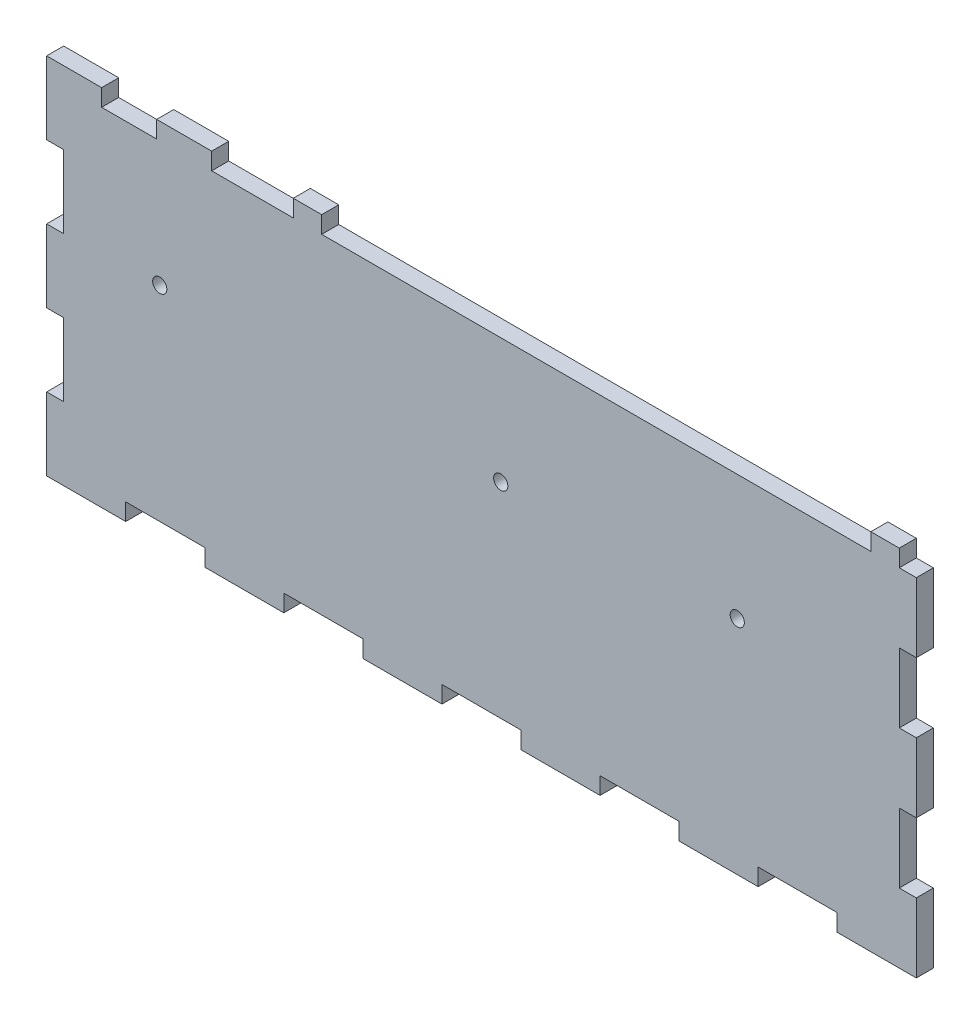
SolidWorks part; units mm, degrees
ref_plane "Alzado" through (0, 0, 0) normal (0, 0, 1) x (1, 0, 0)
ref_plane "Planta" through (0, 0, 0) normal (0, 1, 0) x (1, 0, 0)
ref_plane "Vista lateral" through (0, 0, 0) normal (1, 0, 0) x (0, 0, -1)
sketch "Croquis1" plane through (0, 0, 0) normal (0, 0, 1) x (1, 0, 0)
  line L0 (0, -16.7416) -> (0, -13.7416)
  line L1 (-48.39, -13.7416) -> (0, -13.7416) construction
  line L2 (0, -16.7416) -> (96.61, -16.7416)
  line L3 (101.61, -16.7416) -> (101.61, -49.332) construction
  line L4 (-227.956, -77.7416) -> (93.758, -77.7416) construction
  line L5 (-48.39, -13.7416) -> (-48.39, -77.7416) construction
  line L6 (78.6222, -38.7416) -> (-38.712, -38.7416) construction
  line L7 (0, -13.7416) -> (0, -16.7416) construction
  line L8 (0, -16.7416) -> (-48.39, -16.7416) construction
  line L9 (-48.39, -13.7416) -> (-38.712, -13.7416)
  line L10 (-38.712, -13.7416) -> (-38.712, -16.7416)
  line L11 (-38.712, -16.7416) -> (-29.034, -16.7416)
  line L12 (-29.034, -16.7416) -> (-29.034, -13.7416)
  line L13 (-29.034, -13.7416) -> (-19.356, -13.7416)
  line L14 (-19.356, -13.7416) -> (-19.356, -16.7416)
  line L15 (-19.356, -16.7416) -> (-9.678, -16.7416)
  line L16 (-9.678, -16.7416) -> (-5, -16.7416)
  line L17 (-5, -16.7416) -> (-5, -13.7416)
  line L18 (104.61, -16.7416) -> (104.61, -77.7416) construction
  line L19 (104.61, -16.7416) -> (104.61, -28.9416)
  line L20 (104.61, -28.9416) -> (101.61, -28.9416)
  line L21 (101.61, -28.9416) -> (101.61, -41.1416)
  line L22 (101.61, -41.1416) -> (104.61, -41.1416)
  line L23 (104.61, -41.1416) -> (104.61, -53.3416)
  line L24 (104.61, -53.3416) -> (101.61, -53.3416)
  line L25 (101.61, -53.3416) -> (101.61, -65.5416)
  line L26 (101.61, -65.5416) -> (104.61, -65.5416)
  line L27 (104.61, -65.5416) -> (104.61, -77.7416)
  line L28 (-45.39, -56.5563) -> (-45.39, 45.6638) construction
  line L29 (-48.39, -13.7416) -> (-48.39, -26.5416)
  line L30 (-48.39, -26.5416) -> (-45.39, -26.5416)
  line L31 (-45.39, -26.5416) -> (-45.39, -39.3416)
  line L32 (-45.39, -39.3416) -> (-48.39, -39.3416)
  line L33 (-48.39, -39.3416) -> (-48.39, -52.1416)
  line L34 (-48.39, -52.1416) -> (-45.39, -52.1416)
  line L35 (-45.39, -52.1416) -> (-45.39, -64.9416)
  line L36 (-45.39, -64.9416) -> (-48.39, -64.9416)
  line L37 (-48.39, -64.9416) -> (-48.39, -77.7416)
  line L38 (-102.5031, -74.7416) -> (75.9308, -74.7416) construction
  line L39 (-124.386, -156.1001) -> (179.1879, -156.1001) construction
  line L40 (-48.39, -153.1001) -> (104.61, -153.1001) construction
  line L41 (-48.39, -77.7416) -> (-34.4809, -77.7416)
  line L42 (-34.4809, -77.7416) -> (-34.4809, -74.7416)
  line L43 (-34.4809, -74.7416) -> (-20.5718, -74.7416)
  line L44 (-20.5718, -74.7416) -> (-20.5718, -77.7416)
  line L45 (-20.5718, -77.7416) -> (-6.6627, -77.7416)
  line L46 (-6.6627, -77.7416) -> (-6.6627, -74.7416)
  line L47 (-6.6627, -74.7416) -> (7.2464, -74.7416)
  line L48 (7.2464, -74.7416) -> (7.2464, -77.7416)
  line L49 (7.2464, -77.7416) -> (21.1555, -77.7416)
  line L50 (21.1555, -77.7416) -> (21.1555, -74.7416)
  line L51 (21.1555, -74.7416) -> (35.0645, -74.7416)
  line L52 (35.0645, -74.7416) -> (35.0645, -77.7416)
  line L53 (35.0645, -77.7416) -> (48.9736, -77.7416)
  line L54 (48.9736, -77.7416) -> (48.9736, -74.7416)
  line L55 (48.9736, -74.7416) -> (62.8827, -74.7416)
  line L56 (62.8827, -74.7416) -> (62.8827, -77.7416)
  line L57 (62.8827, -77.7416) -> (76.7918, -77.7416)
  line L58 (76.7918, -77.7416) -> (76.7918, -74.7416)
  line L59 (76.7918, -74.7416) -> (90.7009, -74.7416)
  line L60 (90.7009, -74.7416) -> (90.7009, -77.7416)
  line L61 (90.7009, -77.7416) -> (104.61, -77.7416)
  line L62 (-48.39, -153.1001) -> (-48.39, -260.7101) construction
  line L63 (-48.39, -260.7101) -> (104.61, -260.7101) construction
  line L64 (104.61, -153.1001) -> (104.61, -260.7101) construction
  line L65 (-68.7634, -257.7101) -> (144.8732, -257.7101) construction
  line L66 (101.61, -77.7416) -> (101.61, -269.1968) construction
  line L67 (-45.39, -153.1001) -> (-45.39, -251.8965) construction
  line L68 (-34.4809, -77.7416) -> (-34.4809, -243.0877) construction
  line L69 (-20.5718, -77.7416) -> (-20.5718, -243.0877) construction
  line L70 (-6.6627, -74.7416) -> (-6.6627, -243.0877) construction
  line L71 (7.2464, -74.7416) -> (7.2464, -243.0877) construction
  line L72 (21.1555, -74.7416) -> (21.1555, -243.0877) construction
  line L73 (35.0645, -74.7416) -> (35.0645, -243.0877) construction
  line L74 (48.9736, -74.7416) -> (48.9736, -243.0877) construction
  line L75 (62.8827, -74.7416) -> (62.8827, -243.0877) construction
  line L76 (76.7918, -74.7416) -> (76.7918, -243.0877) construction
  line L77 (90.7009, -74.7416) -> (90.7009, -243.0877) construction
  line L78 (-34.4809, -156.1001) -> (-48.39, -156.1001)
  line L79 (-34.4809, -156.1001) -> (-34.4809, -153.1001)
  line L80 (-34.4809, -153.1001) -> (-20.5718, -153.1001)
  line L81 (-20.5718, -153.1001) -> (-20.5718, -156.1001)
  line L82 (-20.5718, -156.1001) -> (-6.6627, -156.1001)
  line L83 (-6.6627, -156.1001) -> (-6.6627, -153.1001)
  line L84 (-6.6627, -153.1001) -> (7.2464, -153.1001)
  line L85 (7.2464, -153.1001) -> (7.2464, -156.1001)
  line L86 (7.2464, -156.1001) -> (21.1555, -156.1001)
  line L87 (21.1555, -156.1001) -> (21.1555, -153.1001)
  line L88 (21.1555, -153.1001) -> (35.0645, -153.1001)
  line L89 (35.0645, -153.1001) -> (35.0645, -156.1001)
  line L90 (35.0645, -156.1001) -> (48.9736, -156.1001)
  line L91 (48.9736, -156.1001) -> (48.9736, -153.1001)
  line L92 (48.9736, -153.1001) -> (62.8827, -153.1001)
  line L93 (62.8827, -153.1001) -> (62.8827, -156.1001)
  line L94 (62.8827, -156.1001) -> (76.7918, -156.1001)
  line L95 (76.7918, -156.1001) -> (76.7918, -153.1001)
  line L96 (76.7918, -153.1001) -> (90.7009, -153.1001)
  line L97 (90.7009, -153.1001) -> (90.7009, -156.1001)
  line L98 (90.7009, -156.1001) -> (104.61, -156.1001)
  line L99 (-48.39, -257.7101) -> (-34.4809, -257.7101)
  line L100 (-34.4809, -257.7101) -> (-34.4809, -260.7101)
  line L101 (-34.4809, -260.7101) -> (-20.5718, -260.7101)
  line L102 (-20.5718, -260.7101) -> (-20.5718, -257.7101)
  line L103 (-20.5718, -257.7101) -> (-6.6627, -257.7101)
  line L104 (-6.6627, -257.7101) -> (-6.6627, -260.7101)
  line L105 (-6.6627, -260.7101) -> (7.2464, -260.7101)
  line L106 (7.2464, -260.7101) -> (7.2464, -257.7101)
  line L107 (7.2464, -257.7101) -> (21.1555, -257.7101)
  line L108 (21.1555, -257.7101) -> (21.1555, -260.7101)
  line L109 (21.1555, -260.7101) -> (35.0645, -260.7101)
  line L110 (35.0645, -260.7101) -> (35.0645, -257.7101)
  line L111 (35.0645, -257.7101) -> (48.9736, -257.7101)
  line L112 (48.9736, -257.7101) -> (48.9736, -260.7101)
  line L113 (48.9736, -260.7101) -> (62.8827, -260.7101)
  line L114 (62.8827, -260.7101) -> (62.8827, -257.7101)
  line L115 (62.8827, -257.7101) -> (76.7918, -257.7101)
  line L116 (76.7918, -257.7101) -> (76.7918, -260.7101)
  line L117 (76.7918, -260.7101) -> (90.7009, -260.7101)
  line L118 (90.7009, -260.7101) -> (90.7009, -257.7101)
  line L119 (90.7009, -257.7101) -> (104.61, -257.7101)
  line L120 (-226.2526, -13.7416) -> (-226.2526, -77.7416) construction
  line L121 (-290.2526, -77.7416) -> (-226.2526, -77.7416) construction
  line L122 (-226.2526, -77.7416) -> (-226.2526, -287.7111) construction
  line L123 (-290.2526, -77.7416) -> (-290.2526, -287.7111) construction
  line L124 (-290.2526, -287.7111) -> (-226.2526, -287.7111) construction
  line L125 (-48.39, -26.5416) -> (-105.5506, -26.5416) construction
  line L126 (-48.39, -39.3416) -> (-94.7516, -39.3416) construction
  line L127 (-48.39, -52.1416) -> (-71.8061, -52.1416) construction
  line L128 (-48.39, -64.9416) -> (-67.7461, -64.9416) construction
  line L129 (-277.4526, -73.8444) -> (-277.4526, -111.8004) construction
  line L130 (-264.6526, -73.8444) -> (-264.6526, -111.8004) construction
  line L131 (-251.8526, -90.832) -> (-251.8526, -128.788) construction
  line L132 (-239.0526, -73.8444) -> (-239.0526, -111.8004) construction
  line L133 (-229.2526, -73.8444) -> (-229.2526, -93.389) construction
  line L134 (165.3571, -156.1001) -> (174.5571, -156.1001)
  line L135 (174.5571, -156.1001) -> (174.5571, -153.1001)
  line L136 (174.5571, -153.1001) -> (186.7571, -153.1001)
  line L137 (186.7571, -153.1001) -> (186.7571, -156.1001)
  line L138 (186.7571, -156.1001) -> (198.9571, -156.1001)
  line L139 (198.9571, -156.1001) -> (198.9571, -153.1001)
  line L140 (198.9571, -153.1001) -> (211.1571, -153.1001)
  line L141 (211.1571, -153.1001) -> (211.1571, -156.1001)
  line L142 (211.1571, -156.1001) -> (223.3571, -156.1001)
  line L143 (-229.2526, -156.1001) -> (-229.2526, -170.6158)
  line L144 (-229.2526, -170.6158) -> (-226.2526, -170.6158)
  line L145 (-226.2526, -170.6158) -> (-226.2526, -185.1315)
  line L146 (-226.2526, -185.1315) -> (-229.2526, -185.1315)
  line L147 (-229.2526, -185.1315) -> (-229.2526, -199.6473)
  line L148 (-229.2526, -199.6473) -> (-226.2526, -199.6473)
  line L149 (-226.2526, -199.6473) -> (-226.2526, -220.163)
  line L150 (-226.2526, -220.163) -> (-229.2526, -220.163)
  line L151 (-48.39, -257.7101) -> (-48.39, -243.1944)
  line L152 (-48.39, -243.1944) -> (-45.39, -243.1944)
  line L153 (-45.39, -243.1944) -> (-45.39, -228.6787)
  line L154 (-45.39, -228.6787) -> (-48.39, -228.6787)
  line L155 (-48.39, -228.6787) -> (-48.39, -214.163)
  line L156 (-48.39, -214.163) -> (-45.39, -214.163)
  line L157 (-45.39, -214.163) -> (-45.39, -199.6473)
  line L158 (-45.39, -199.6473) -> (-48.39, -199.6473)
  line L159 (-48.39, -199.6473) -> (-48.39, -185.1315)
  line L160 (-48.39, -185.1315) -> (-45.39, -185.1315)
  line L161 (-45.39, -185.1315) -> (-45.39, -170.6158)
  line L162 (-45.39, -170.6158) -> (-48.39, -170.6158)
  line L163 (-48.39, -170.6158) -> (-48.39, -156.1001)
  line L164 (-48.39, -228.6787) -> (-80.3979, -228.6787) construction
  line L165 (-48.39, -243.1944) -> (-76.899, -243.1944) construction
  line L166 (-48.39, -214.163) -> (-74.7996, -214.163) construction
  line L167 (-48.39, -199.6473) -> (-74.7996, -199.6473) construction
  line L168 (-74.7996, -185.1315) -> (-48.39, -185.1315) construction
  line L169 (-48.39, -170.6158) -> (-71.0675, -170.6158) construction
  line L170 (-229.2526, -220.163) -> (-229.2526, -234.6787)
  line L171 (-287.2526, -73.8444) -> (-287.2526, -109.848) construction
  line L172 (-229.2526, -234.6787) -> (-226.2526, -234.6787)
  line L173 (-226.2526, -234.6787) -> (-226.2526, -249.1944)
  line L174 (-226.2526, -249.1944) -> (-229.2526, -249.1944)
  line L175 (-229.2526, -249.1944) -> (-229.2526, -257.7101)
  line L176 (223.3571, -257.7101) -> (211.1571, -257.7101)
  line L177 (211.1571, -257.7101) -> (211.1571, -260.7101)
  line L178 (211.1571, -260.7101) -> (198.9571, -260.7101)
  line L179 (198.9571, -260.7101) -> (198.9571, -257.7101)
  line L180 (198.9571, -257.7101) -> (186.7571, -257.7101)
  line L181 (186.7571, -257.7101) -> (186.7571, -260.7101)
  line L182 (186.7571, -260.7101) -> (174.5571, -260.7101)
  line L183 (174.5571, -260.7101) -> (174.5571, -257.7101)
  line L184 (-287.2526, -257.7101) -> (-287.2526, -243.1944)
  line L185 (-287.2526, -243.1944) -> (-290.2526, -243.1944)
  line L186 (-290.2526, -243.1944) -> (-290.2526, -228.6787)
  line L187 (-290.2526, -228.6787) -> (-287.2526, -228.6787)
  line L188 (-287.2526, -228.6787) -> (-287.2526, -214.163)
  line L189 (-287.2526, -214.163) -> (-290.2526, -214.163)
  line L190 (-290.2526, -214.163) -> (-290.2526, -199.6473)
  line L191 (-290.2526, -199.6473) -> (-287.2526, -199.6473)
  line L192 (-287.2526, -199.6473) -> (-287.2526, -185.1315)
  line L193 (-287.2526, -185.1315) -> (-290.2526, -185.1315)
  line L194 (-290.2526, -185.1315) -> (-290.2526, -170.6158)
  line L195 (-290.2526, -170.6158) -> (-287.2526, -170.6158)
  line L196 (-287.2526, -170.6158) -> (-287.2526, -156.1001)
  line L197 (174.5571, -257.7101) -> (165.3571, -257.7101)
  line L198 (-315.487, -120.5373) -> (-315.487, -274.6014) construction
  line L199 (-423.097, -153.1001) -> (-423.097, -80.2802) construction
  line L200 (-420.097, -153.1001) -> (-420.097, -73.0846) construction
  line L201 (-405.5813, -153.1001) -> (-405.5813, -73.0846) construction
  line L202 (-391.0655, -153.1001) -> (-391.0655, -77.6291) construction
  line L203 (-376.5498, -153.1001) -> (-376.5498, -80.2802) construction
  line L204 (-362.0341, -153.1001) -> (-362.0341, -73.0846) construction
  line L205 (-347.5184, -153.1001) -> (-347.5184, -77.6291) construction
  line L206 (-333.0027, -153.1001) -> (-333.0027, -73.0846) construction
  line L207 (-318.487, -153.1001) -> (-318.487, -77.6291) construction
  line L208 (-48.39, -21.6772) -> (-48.39, 38.9813) construction
  line L209 (-38.712, -13.7416) -> (-38.712, 45.6638) construction
  line L210 (-29.034, -13.7416) -> (-29.034, 45.6638) construction
  line L211 (-19.356, -13.7416) -> (-19.356, 45.6638) construction
  line L212 (-9.678, -13.7416) -> (-9.678, 45.6638) construction
  line L213 (0, -13.7416) -> (0, 45.6638) construction
  line L214 (2.5149, 38.1832) -> (-48.39, 38.1832) construction
  line L215 (-48.39, 86.5732) -> (-80.1148, 86.5732) construction
  line L216 (-48.39, 76.8952) -> (-75.2531, 76.8952) construction
  line L217 (-48.39, 67.2172) -> (-75.2531, 67.2172) construction
  line L218 (-48.39, 57.5392) -> (-80.1148, 57.5392) construction
  line L219 (-48.39, 47.8612) -> (-84.9766, 47.8612) construction
  line L220 (-318.487, 38.1832) -> (-318.487, 47.8612)
  line L221 (-48.39, 38.1832) -> (-76.9441, 38.1832) construction
  line L222 (-318.487, 47.8612) -> (-315.487, 47.8612)
  line L223 (-315.487, 47.8612) -> (-315.487, 57.5392)
  line L224 (-315.487, 57.5392) -> (-318.487, 57.5392)
  line L225 (-318.487, 57.5392) -> (-318.487, 67.2172)
  line L226 (-318.487, 67.2172) -> (-315.487, 67.2172)
  line L227 (-315.487, 67.2172) -> (-315.487, 76.8952)
  line L228 (-315.487, 76.8952) -> (-318.487, 76.8952)
  line L229 (-318.487, 76.8952) -> (-318.487, 86.5732)
  line L230 (-318.487, 86.5732) -> (-420.097, 86.5732)
  line L231 (-420.097, 86.5732) -> (-420.097, 76.8952)
  line L232 (-420.097, 76.8952) -> (-423.097, 76.8952)
  line L233 (-423.097, 76.8952) -> (-423.097, 67.2172)
  line L234 (-423.097, 67.2172) -> (-420.097, 67.2172)
  line L235 (-420.097, 67.2172) -> (-420.097, 57.5392)
  line L236 (-420.097, 57.5392) -> (-423.097, 57.5392)
  line L237 (-423.097, 57.5392) -> (-423.097, 47.8612)
  line L238 (-423.097, 47.8612) -> (-420.097, 47.8612)
  line L239 (-420.097, 47.8612) -> (-420.097, 38.1832)
  line L240 (-48.39, 41.1832) -> (-83.9517, 41.1832) construction
  line L241 (-318.487, 38.1832) -> (-333.0027, 38.1832)
  line L242 (-333.0027, 38.1832) -> (-333.0027, 41.1832)
  line L243 (-333.0027, 41.1832) -> (-347.5184, 41.1832)
  line L244 (-347.5184, 41.1832) -> (-347.5184, 38.1832)
  line L245 (-347.5184, 38.1832) -> (-362.0341, 38.1832)
  line L246 (-362.0341, 38.1832) -> (-362.0341, 41.1832)
  line L247 (-362.0341, 41.1832) -> (-376.5498, 41.1832)
  line L248 (-376.5498, 41.1832) -> (-376.5498, 38.1832)
  line L249 (-376.5498, 38.1832) -> (-391.0655, 38.1832)
  line L250 (-391.0655, 38.1832) -> (-391.0655, 41.1832)
  line L251 (-391.0655, 41.1832) -> (-405.5813, 41.1832)
  line L252 (-405.5813, 41.1832) -> (-405.5813, 38.1832)
  line L253 (-405.5813, 38.1832) -> (-420.097, 38.1832)
  line L254 (162.3571, -15.1529) -> (162.3571, -104.9762) construction
  line L255 (104.61, -28.9416) -> (145.8916, -28.9416) construction
  line L256 (104.61, -41.1416) -> (145.8916, -41.1416) construction
  line L257 (104.61, -65.5416) -> (131.4417, -65.5416) construction
  line L258 (104.61, -53.3416) -> (126.5441, -53.3416) construction
  line L259 (165.3571, -73.8444) -> (165.3571, -106.8492) construction
  line L260 (174.5571, -73.8444) -> (174.5571, -108.8044) construction
  line L261 (186.7571, -73.8444) -> (186.7571, -108.8044) construction
  line L262 (198.9571, -73.8444) -> (198.9571, -108.8044) construction
  line L263 (211.1571, -73.8444) -> (211.1571, -106.8492) construction
  line L264 (223.3571, -73.8444) -> (223.3571, -108.8044) construction
  line L265 (104.61, -257.7101) -> (104.61, -243.0877)
  line L266 (104.61, -243.0877) -> (101.61, -243.0877)
  line L267 (101.61, -243.0877) -> (101.61, -228.6787)
  line L268 (101.61, -228.6787) -> (104.61, -228.6787)
  line L269 (104.61, -228.6787) -> (104.61, -214.163)
  line L270 (104.61, -214.163) -> (101.61, -214.163)
  line L271 (101.61, -214.163) -> (101.61, -199.6473)
  line L272 (101.61, -199.6473) -> (104.61, -199.6473)
  line L273 (104.61, -199.6473) -> (104.61, -185.1315)
  line L274 (104.61, -185.1315) -> (101.61, -185.1315)
  line L275 (101.61, -185.1315) -> (101.61, -170.6158)
  line L276 (101.61, -170.6158) -> (104.61, -170.6158)
  line L277 (104.61, -170.6158) -> (104.61, -156.1001)
  line L278 (-229.2526, -156.1001) -> (-239.0526, -156.1001)
  line L279 (-239.0526, -156.1001) -> (-239.0526, -153.1001)
  line L280 (-239.0526, -153.1001) -> (-251.8526, -153.1001)
  line L281 (-251.8526, -153.1001) -> (-251.8526, -156.1001)
  line L282 (-251.8526, -156.1001) -> (-264.6526, -156.1001)
  line L283 (-264.6526, -156.1001) -> (-264.6526, -153.1001)
  line L284 (-264.6526, -153.1001) -> (-277.4526, -153.1001)
  line L285 (-277.4526, -153.1001) -> (-277.4526, -156.1001)
  line L286 (-277.4526, -156.1001) -> (-287.2526, -156.1001)
  line L287 (223.3571, -156.1001) -> (223.3571, -257.7101)
  line L288 (-229.2526, -257.7101) -> (-239.0526, -257.7101)
  line L289 (-239.0526, -257.7101) -> (-239.0526, -260.7101)
  line L290 (-239.0526, -260.7101) -> (-251.8526, -260.7101)
  line L291 (-251.8526, -260.7101) -> (-251.8526, -257.7101)
  line L292 (-251.8526, -257.7101) -> (-264.6526, -257.7101)
  line L293 (-264.6526, -257.7101) -> (-264.6526, -260.7101)
  line L294 (-264.6526, -260.7101) -> (-277.4526, -260.7101)
  line L295 (-277.4526, -260.7101) -> (-277.4526, -257.7101)
  line L296 (-277.4526, -257.7101) -> (-287.2526, -257.7101)
  line L297 (165.3571, -257.7101) -> (165.3571, -243.1944)
  line L298 (165.3571, -243.1944) -> (162.3571, -243.1944)
  line L299 (162.3571, -243.1944) -> (162.3571, -228.6787)
  line L300 (162.3571, -228.6787) -> (165.3571, -228.6787)
  line L301 (165.3571, -228.6787) -> (165.3571, -214.163)
  line L302 (165.3571, -214.163) -> (162.3571, -214.163)
  line L303 (162.3571, -214.163) -> (162.3571, -199.6473)
  line L304 (162.3571, -199.6473) -> (165.3571, -199.6473)
  line L305 (165.3571, -199.6473) -> (165.3571, -185.1315)
  line L306 (165.3571, -185.1315) -> (162.3571, -185.1315)
  line L307 (162.3571, -185.1315) -> (162.3571, -170.6158)
  line L308 (162.3571, -170.6158) -> (165.3571, -170.6158)
  line L309 (165.3571, -170.6158) -> (165.3571, -156.1001)
  line L310 (-5, -13.7416) -> (0, -13.7416)
  line L311 (96.61, -16.7416) -> (96.61, -13.7416)
  line L312 (96.61, -13.7416) -> (101.61, -13.7416)
  line L313 (101.61, -13.7416) -> (101.61, -16.7416)
  line L314 (101.61, -16.7416) -> (104.61, -16.7416)
  circle A0 centre (73.11, -38.7416) radius 1.25
  circle A1 centre (31.5, -38.7416) radius 1.25
  circle A2 centre (-28.49, -38.7416) radius 1.25
  arc A3 (-226.2526, -64.9416) -> (-239.0526, -77.7416) centre (-226.2526, -77.7416) ccw construction
  arc A4 (-226.2526, -52.1416) -> (-251.8526, -77.7416) centre (-226.2526, -77.7416) ccw construction
  arc A5 (-226.2526, -39.3416) -> (-264.6526, -77.7416) centre (-226.2526, -77.7416) ccw construction
  arc A6 (-226.2526, -26.5416) -> (-277.4526, -77.7416) centre (-226.2526, -77.7416) ccw construction
  arc A7 (-226.2526, -13.7416) -> (-290.2526, -77.7416) centre (-226.2526, -77.7416) ccw construction
  arc A8 (-226.2526, -74.7416) -> (-229.2526, -77.7416) centre (-226.2526, -77.7416) ccw construction
  arc A9 (-226.2526, -16.7416) -> (-287.2526, -77.7416) centre (-226.2526, -77.7416) ccw construction
  arc A10 (-315.487, -156.1001) -> (-318.487, -153.1001) centre (-315.487, -153.1001) cw construction
  arc A11 (-315.487, -170.6158) -> (-333.0027, -153.1001) centre (-315.487, -153.1001) cw construction
  arc A12 (-315.487, -185.1315) -> (-347.5184, -153.1001) centre (-315.487, -153.1001) cw construction
  arc A13 (-315.487, -199.6473) -> (-362.0341, -153.1001) centre (-315.487, -153.1001) cw construction
  arc A14 (-315.487, -214.163) -> (-376.5498, -153.1001) centre (-315.487, -153.1001) cw construction
  arc A15 (-315.487, -228.6787) -> (-391.0655, -153.1001) centre (-315.487, -153.1001) cw construction
  arc A16 (-315.487, -243.1944) -> (-405.5813, -153.1001) centre (-315.487, -153.1001) cw construction
  arc A17 (-315.487, -257.7101) -> (-420.097, -153.1001) centre (-315.487, -153.1001) cw construction
  arc A18 (-315.487, -260.7101) -> (-423.097, -153.1001) centre (-315.487, -153.1001) cw construction
  arc A19 (-45.39, 38.1832) -> (-48.39, 41.1832) centre (-48.39, 38.1832) ccw construction
  arc A20 (-38.712, 38.1832) -> (-48.39, 47.8612) centre (-48.39, 38.1832) ccw construction
  arc A21 (-29.034, 38.1832) -> (-48.39, 57.5392) centre (-48.39, 38.1832) ccw construction
  arc A22 (-19.356, 38.1832) -> (-48.39, 67.2172) centre (-48.39, 38.1832) ccw construction
  arc A23 (-9.678, 38.1832) -> (-48.39, 76.8952) centre (-48.39, 38.1832) ccw construction
  arc A24 (0, 38.1832) -> (-48.39, 86.5732) centre (-48.39, 38.1832) ccw construction
  arc A25 (162.3571, -74.7416) -> (165.3571, -77.7416) centre (162.3571, -77.7416) cw construction
  arc A26 (162.3571, -65.5416) -> (174.5571, -77.7416) centre (162.3571, -77.7416) cw construction
  arc A27 (162.3571, -53.3416) -> (186.7571, -77.7416) centre (162.3571, -77.7416) cw construction
  arc A28 (162.3571, -41.1416) -> (198.9571, -77.7416) centre (162.3571, -77.7416) cw construction
  arc A29 (162.3571, -28.9416) -> (211.1571, -77.7416) centre (162.3571, -77.7416) cw construction
  arc A30 (162.3571, -16.7416) -> (223.3571, -77.7416) centre (162.3571, -77.7416) cw construction
  text T0 "TOP\r\n"
  dimension "D2" = 2.5
  dimension "D3" = 2.5
  dimension "D4" = 2.5
  dimension "D7" = 101.6
  dimension "D9" = 36
  dimension "D1" = 153
  dimension "D5" = 3
  dimension "D6" = 104.61
  dimension "D8" = 3
  dimension "D10" = 3
  dimension "D11" = 41.61
  dimension "D12" = 5
  dimension "D13" = 3
  dimension "D14" = 153
  dimension "D15" = 107.61
  dimension "D16" = 5
  dimension "D17" = 3
  dimension "D18" = 3
  dimension "D19" = 28.5
extrude "Saliente-Extruir1" add sketch "Croquis1" along normal blind 3
